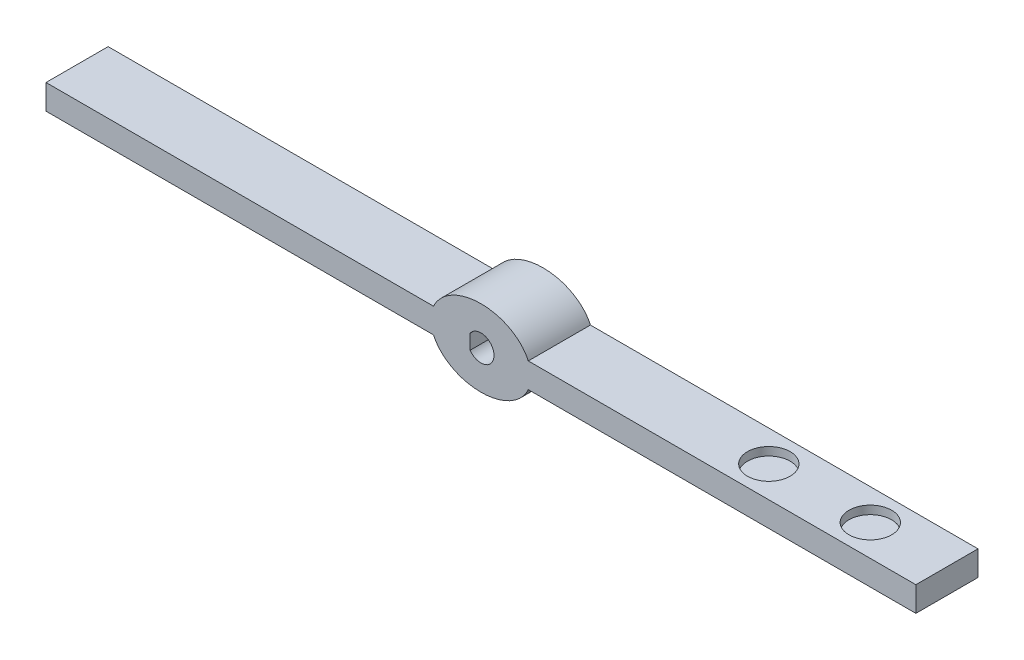
SolidWorks part; units mm, degrees
ref_plane "Front Plane" through (0, 0, 0) normal (0, 0, 1) x (1, 0, 0)
ref_plane "Top Plane" through (0, 0, 0) normal (0, 1, 0) x (1, 0, 0)
ref_plane "Right Plane" through (0, 0, 0) normal (1, 0, 0) x (0, 0, -1)
sketch "Sketch1" plane through (0, 0, 0) normal (0, 0, 1) x (1, 0, 0)
  line L1 (-85.2553, 21.1831) -> (124.7447, 21.1831)
  line L2 (-85.2553, 21.1831) -> (-85.2553, 15.1831)
  line L3 (-85.2553, 15.1831) -> (124.7447, 15.1831)
  line L4 (124.7447, 21.1831) -> (124.7447, 15.1831)
  dimension "D1" = 210
  dimension "D2" = 6
extrude "Boss-Extrude1" add sketch "Sketch1" along normal blind 15
sketch "Sketch2" plane through (0, 0, 15) normal (0, 0, 1) x (1, 0, 0)
  line L0 (-85.2553, 18.1831) -> (124.7447, 18.1831) construction
  line L1 (-85.2553, 21.1831) -> (-85.2553, 15.1831) construction
  line L2 (124.7447, 15.1831) -> (124.7447, 21.1831) construction
  line L3 (19.7447, 21.1831) -> (19.7447, 15.1831) construction
  line L4 (124.7447, 21.1831) -> (-85.2553, 21.1831) construction
  line L5 (-85.2553, 15.1831) -> (124.7447, 15.1831) construction
  ellipse E0 centre (19.7447, 18.1831) end of major axis (31.8295, 18.1831) minor radius 9.2594
extrude "Boss-Extrude2" add sketch "Sketch2" against normal blind 15
sketch "Sketch3" plane through (0, 0, 15) normal (0, 0, 1) x (1, 0, 0)
  line L0 (19.7447, 27.4425) -> (19.7447, 8.9236) construction
  circle A0 centre (19.7447, 18.1831) radius 3.15
  ellipse E0 centre (19.7447, 18.1831) end of major axis (31.8295, 18.1831) minor radius 9.2594 (31.1776, 21.1831) -> (8.3118, 21.1831) ccw construction
  ellipse E1 centre (19.7447, 18.1831) end of major axis (31.8295, 18.1831) minor radius 9.2594 (8.3118, 15.1831) -> (31.1776, 15.1831) ccw construction
extrude "Cut-Extrude1" cut sketch "Sketch3" against normal blind 15
sketch "Sketch4" plane through (0, 0, 15) normal (0, 0, 1) x (1, 0, 0)
  line L0 (17.1447, 19.9614) -> (17.1447, 16.4047)
  line L1 (19.7447, 18.1831) -> (22.8947, 18.1831) construction
  circle A0 centre (19.7447, 18.1831) radius 3.15 construction
  arc A1 (17.1447, 19.9614) -> (17.1447, 16.4047) centre (19.6839, 18.1831) ccw
  dimension "D1" = 2.6
extrude "Boss-Extrude3" add sketch "Sketch4" against normal blind 15
sketch "Sketch5" plane through (0, 15.1831, 0) normal (0, -1, 0) x (1, 0, 0)
  line L0 (19.7447, 15) -> (19.7447, 0) construction
  line L1 (31.1776, 15) -> (8.3118, 15) construction
  line L2 (8.3118, 0) -> (31.1776, 0) construction
  line L3 (-85.2553, 7.5) -> (124.7447, 7.5) construction
  line L4 (-85.2553, 15) -> (-85.2553, 0) construction
  line L5 (124.7447, 15) -> (124.7447, 0) construction
  circle A0 centre (-42.2553, 7.5) radius 5.15
  circle A1 centre (-66.7553, 7.5) radius 5.15
  point P14 (19.7447, 7.5)
  dimension "D1" = 62
  dimension "D2" = 2
extrude "Cut-Extrude2" cut sketch "Sketch5" against normal blind 2
sketch "Sketch6" plane through (0, 21.1831, 0) normal (0, 1, 0) x (1, 0, 0)
  line L0 (19.7447, 0) -> (19.7447, -15) construction
  line L1 (31.1776, 0) -> (8.3118, 0) construction
  line L2 (8.3118, -15) -> (31.1776, -15) construction
  line L3 (19.7447, -7.5) -> (124.7447, -7.5) construction
  line L4 (124.7447, -15) -> (124.7447, 0) construction
  circle A0 centre (81.7447, -7.5) radius 5.15
  circle A1 centre (106.2447, -7.5) radius 5.15
  dimension "D1" = 62
  dimension "D2" = 2
extrude "Cut-Extrude3" cut sketch "Sketch6" against normal blind 2
